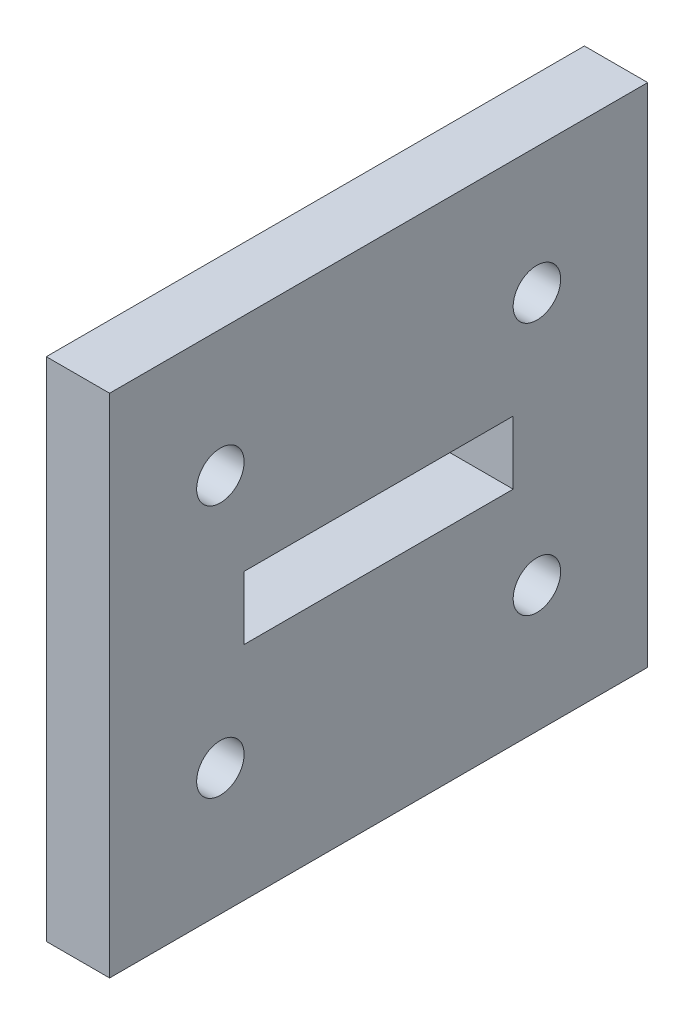
SolidWorks part; units mm, degrees
ref_plane "Спереди" through (0, 0, 0) normal (0, 0, 1) x (1, 0, 0)
ref_plane "Сверху" through (0, 0, 0) normal (0, 1, 0) x (1, 0, 0)
ref_plane "Справа" through (0, 0, 0) normal (1, 0, 0) x (0, 0, -1)
ref_plane "Плоскость4" through (25.2, 0, 0) normal (1, 0, 0) x (0, 0, -1)
sketch "Эскиз1" plane through (25.2, 0, 0) normal (1, 0, 0) x (0, 0, -1)
  line L4 (-13.2363, 7.4936) -> (20.7637, 7.4936)
  line L5 (20.7637, 7.4936) -> (20.7637, 39.4936)
  line L6 (20.7637, 39.4936) -> (-13.2363, 39.4936)
  line L7 (-13.2363, 39.4936) -> (-13.2363, 7.4936)
  line L8 (-13.2363, 7.4936) -> (20.7637, 7.4936)
  line L9 (20.7637, 7.4936) -> (20.7637, 39.4936)
  line L10 (20.7637, 39.4936) -> (-13.2363, 39.4936)
  line L11 (-13.2363, 39.4936) -> (-13.2363, 7.4936)
  circle A0 centre (-6.2363, 31.4936) radius 1.5 construction
  circle A1 centre (13.7637, 31.4936) radius 1.5 construction
  circle A2 centre (-6.2363, 15.4936) radius 1.5 construction
  circle A3 centre (13.7637, 15.4936) radius 1.5 construction
  circle A4 centre (-6.2363, 31.4936) radius 1.5
  circle A5 centre (13.7637, 31.4936) radius 1.5
  circle A6 centre (-6.2363, 15.4936) radius 1.5
  circle A7 centre (13.7637, 15.4936) radius 1.5
  dimension "D1" = 0
extrude "Бобышка-Вытянуть1" add sketch "Эскиз1" along normal blind 4
sketch "Эскиз2" plane through (29.2, 0, 0) normal (1, 0, 0) x (0, 0, -1)
  line L0 (-4.7363, 25.4936) -> (12.2637, 25.4936)
  line L1 (-4.7363, 25.4936) -> (-4.7363, 21.4936)
  line L2 (12.2637, 25.4936) -> (12.2637, 21.4936)
  line L3 (-4.7363, 21.4936) -> (12.2637, 21.4936)
  line L4 (3.7637, 39.4936) -> (3.7637, 7.4936) construction
  line L5 (20.7637, 39.4936) -> (-13.2363, 39.4936) construction
  line L6 (-13.2363, 7.4936) -> (20.7637, 7.4936) construction
  line L7 (20.7637, 23.4936) -> (-13.2363, 23.4936) construction
  line L8 (20.7637, 7.4936) -> (20.7637, 39.4936) construction
  line L9 (-13.2363, 39.4936) -> (-13.2363, 7.4936) construction
  line L10 (12.2637, 23.4936) -> (-4.7363, 23.4936) construction
  line L11 (3.7637, 25.4936) -> (3.7637, 21.4936) construction
  dimension "D2" = 4
  dimension "D1" = 17
extrude "Вырез-Вытянуть1" cut sketch "Эскиз2" against normal through all
